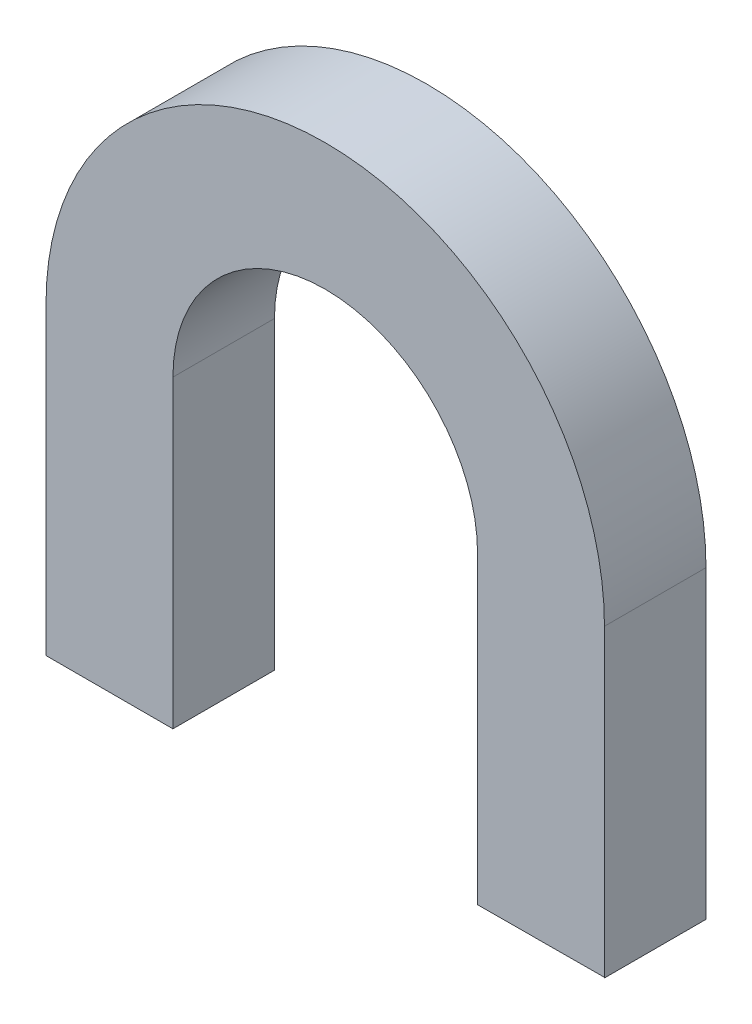
SolidWorks part; units mm, degrees
ref_plane "Front Plane" through (0, 0, 0) normal (0, 0, 1) x (1, 0, 0)
ref_plane "Top Plane" through (0, 0, 0) normal (0, 1, 0) x (1, 0, 0)
ref_plane "Right Plane" through (0, 0, 0) normal (1, 0, 0) x (0, 0, -1)
sketch "Sketch2" plane through (0, 0, 0) normal (0, 0, 1) x (1, 0, 0)
  line L0 (-37.4119, 35.1875) -> (-37.4119, 23.1875)
  line L1 (-59.4119, 35.1875) -> (-59.4119, 23.1875)
  line L2 (-54.4119, 35.1875) -> (-54.4119, 23.1875)
  line L3 (-59.4119, 23.1875) -> (-54.4119, 23.1875)
  line L4 (-42.4119, 35.1875) -> (-42.4119, 23.1875)
  line L5 (-42.4119, 23.1875) -> (-37.4406, 23.2093)
  line L6 (-37.4119, 23.1875) -> (-37.4406, 23.2093)
  line L7 (-37.4119, 35.1875) -> (-37.4119, 23.1875) construction
  arc A0 (-42.4119, 35.1875) -> (-54.4119, 35.1875) centre (-48.4119, 35.1875) ccw
  arc A1 (-37.4119, 35.1875) -> (-59.4119, 35.1875) centre (-48.4119, 35.1875) ccw
  dimension "D1" = 5
  dimension "D3" = 6
  dimension "D2" = 4.9712
  dimension "D4" = 12
extrude "Boss-Extrude1" add sketch "Sketch2" along normal blind 4 contours A0 L2 L3 L1 A1 L0 L6 L5 L4
